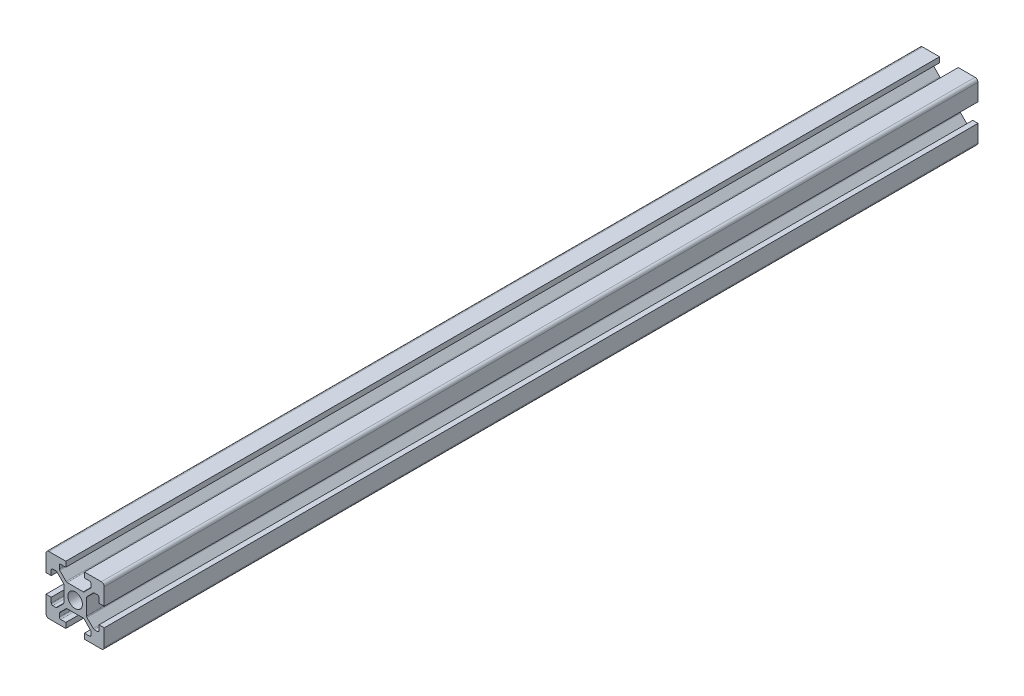
SolidWorks part; units mm, degrees
ref_plane "Front Plane" through (0, 0, 0) normal (0, 0, 1) x (1, 0, 0)
ref_plane "Top Plane" through (0, 0, 0) normal (0, 1, 0) x (1, 0, 0)
ref_plane "Right Plane" through (0, 0, 0) normal (1, 0, 0) x (0, 0, -1)
ref_plane "Plane1" through (0, 0, 0) normal (0, 0, -1) x (-1, 0, 0)
sketch "Sketch1" plane through (0, 0, 0) normal (0, 0, -1) x (-1, 0, 0)
  line L0 (-20, 19) -> (-20, 13.2)
  line L1 (-20, 13.2) -> (-18.2, 13.2)
  line L2 (-18.2, 13.2) -> (-18.2, 14.95)
  line L3 (-17.7, 15.45) -> (-16.6071, 15.45)
  line L4 (-16.2536, 15.3036) -> (-14.0464, 13.0964)
  line L5 (-13.9, 12.7429) -> (-13.9, 7.2571)
  line L6 (-14.0464, 6.9036) -> (-16.2536, 4.6964)
  line L7 (-16.6071, 4.55) -> (-17.7, 4.55)
  line L8 (-18.2, 5.05) -> (-18.2, 6.8)
  line L9 (-18.2, 6.8) -> (-20, 6.8)
  line L10 (-20, 6.8) -> (-20, 1)
  line L11 (-19, 0) -> (-13.2, 0)
  line L12 (-13.2, 0) -> (-13.2, 1.8)
  line L13 (-13.2, 1.8) -> (-14.95, 1.8)
  line L14 (-15.45, 2.3) -> (-15.45, 3.3929)
  line L15 (-15.3036, 3.7464) -> (-13.0964, 5.9536)
  line L16 (-12.7429, 6.1) -> (-7.2571, 6.1)
  line L17 (-6.9036, 5.9536) -> (-4.6964, 3.7464)
  line L18 (-4.55, 3.3929) -> (-4.55, 2.3)
  line L19 (-5.05, 1.8) -> (-6.8, 1.8)
  line L20 (-6.8, 1.8) -> (-6.8, 0)
  line L21 (-6.8, 0) -> (-1, 0)
  line L22 (0, 1) -> (0, 6.8)
  line L23 (0, 6.8) -> (-1.8, 6.8)
  line L24 (-1.8, 6.8) -> (-1.8, 5.05)
  line L25 (-2.3, 4.55) -> (-3.3929, 4.55)
  line L26 (-3.7464, 4.6964) -> (-5.9536, 6.9036)
  line L27 (-6.1, 7.2571) -> (-6.1, 12.7429)
  line L28 (-5.9536, 13.0964) -> (-3.7464, 15.3036)
  line L29 (-3.3929, 15.45) -> (-2.3, 15.45)
  line L30 (-1.8, 14.95) -> (-1.8, 13.2)
  line L31 (-1.8, 13.2) -> (0, 13.2)
  line L32 (0, 13.2) -> (0, 19)
  line L33 (-1, 20) -> (-6.8, 20)
  line L34 (-6.8, 20) -> (-6.8, 18.2)
  line L35 (-6.8, 18.2) -> (-5.05, 18.2)
  line L36 (-4.55, 17.7) -> (-4.55, 16.6071)
  line L37 (-4.6964, 16.2536) -> (-6.9036, 14.0464)
  line L38 (-7.2571, 13.9) -> (-12.7429, 13.9)
  line L39 (-13.0964, 14.0464) -> (-15.3036, 16.2536)
  line L40 (-15.45, 16.6071) -> (-15.45, 17.7)
  line L41 (-14.95, 18.2) -> (-13.2, 18.2)
  line L42 (-13.2, 18.2) -> (-13.2, 20)
  line L43 (-13.2, 20) -> (-19, 20)
  circle A0 centre (-10, 10) radius 2.5
  arc A1 (-19, 20) -> (-20, 19) centre (-19, 19) ccw
  arc A2 (-18.2, 14.95) -> (-17.7, 15.45) centre (-17.7, 14.95) cw
  arc A3 (-16.6071, 15.45) -> (-16.2536, 15.3036) centre (-16.6071, 14.95) cw
  arc A4 (-14.0464, 13.0964) -> (-13.9, 12.7429) centre (-14.4, 12.7429) cw
  arc A5 (-13.9, 7.2571) -> (-14.0464, 6.9036) centre (-14.4, 7.2571) cw
  arc A6 (-16.2536, 4.6964) -> (-16.6071, 4.55) centre (-16.6071, 5.05) cw
  arc A7 (-17.7, 4.55) -> (-18.2, 5.05) centre (-17.7, 5.05) cw
  arc A8 (-20, 1) -> (-19, 0) centre (-19, 1) ccw
  arc A9 (-14.95, 1.8) -> (-15.45, 2.3) centre (-14.95, 2.3) cw
  arc A10 (-15.45, 3.3929) -> (-15.3036, 3.7464) centre (-14.95, 3.3929) cw
  arc A11 (-13.0964, 5.9536) -> (-12.7429, 6.1) centre (-12.7429, 5.6) cw
  arc A12 (-7.2571, 6.1) -> (-6.9036, 5.9536) centre (-7.2571, 5.6) cw
  arc A13 (-4.6964, 3.7464) -> (-4.55, 3.3929) centre (-5.05, 3.3929) cw
  arc A14 (-4.55, 2.3) -> (-5.05, 1.8) centre (-5.05, 2.3) cw
  arc A15 (-1, 0) -> (0, 1) centre (-1, 1) ccw
  arc A16 (-1.8, 5.05) -> (-2.3, 4.55) centre (-2.3, 5.05) cw
  arc A17 (-3.3929, 4.55) -> (-3.7464, 4.6964) centre (-3.3929, 5.05) cw
  arc A18 (-5.9536, 6.9036) -> (-6.1, 7.2571) centre (-5.6, 7.2571) cw
  arc A19 (-6.1, 12.7429) -> (-5.9536, 13.0964) centre (-5.6, 12.7429) cw
  arc A20 (-3.7464, 15.3036) -> (-3.3929, 15.45) centre (-3.3929, 14.95) cw
  arc A21 (-2.3, 15.45) -> (-1.8, 14.95) centre (-2.3, 14.95) cw
  arc A22 (0, 19) -> (-1, 20) centre (-1, 19) ccw
  arc A23 (-5.05, 18.2) -> (-4.55, 17.7) centre (-5.05, 17.7) cw
  arc A24 (-4.55, 16.6071) -> (-4.6964, 16.2536) centre (-5.05, 16.6071) cw
  arc A25 (-6.9036, 14.0464) -> (-7.2571, 13.9) centre (-7.2571, 14.4) cw
  arc A26 (-12.7429, 13.9) -> (-13.0964, 14.0464) centre (-12.7429, 14.4) cw
  arc A27 (-15.3036, 16.2536) -> (-15.45, 16.6071) centre (-14.95, 16.6071) cw
  arc A28 (-15.45, 17.7) -> (-14.95, 18.2) centre (-14.95, 17.7) cw
extrude "Boss-Extrude1" add sketch "Sketch1" against normal blind 300
